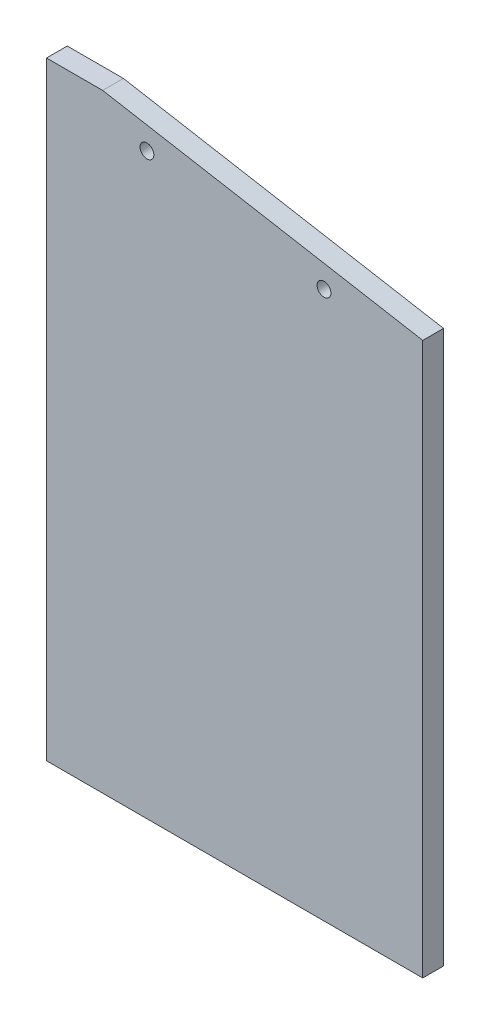
SolidWorks part; units mm, degrees
material "Pine"
ref_plane "Front Plane" through (0, 0, 0) normal (0, 0, 1) x (1, 0, 0)
ref_plane "Top Plane" through (0, 0, 0) normal (0, 1, 0) x (1, 0, 0)
ref_plane "Right Plane" through (0, 0, 0) normal (1, 0, 0) x (0, 0, -1)
sketch "Sketch1" plane through (0, 0, 0) normal (0, 0, 1) x (1, 0, 0)
  line L0 (151.0236, 150.9529) -> (-32.6409, 183.3379)
  line L1 (-64.8764, 183.3379) -> (-32.6409, 183.3379)
  line L2 (-64.8764, 183.3379) -> (-64.8764, -413.5621)
  line L3 (-64.8764, -413.5621) -> (-32.6409, -413.5621)
  line L4 (151.0236, 150.9529) -> (151.0236, -381.1771)
  line L5 (151.0236, -115.1121) -> (-64.8764, -115.1121) construction
  line L6 (151.0236, -381.1771) -> (-32.6409, -413.5621)
  dimension "D1" = 532.13
  dimension "D2" = 215.9
  dimension "D3" = 170
  dimension "D4" = 596.9
extrude "Boss-Extrude1" add sketch "Sketch1" along normal blind 11.9062
hole_wizard "5/16 (0.3125) Diameter Hole1" positions "Sketch2" profile "Sketch3" hole size "5/16" standard "ANSI Inch" end condition through all
sketch "Sketch2" plane through (0, 0, 11.9062) normal (0, 0, 1) x (1, 0, 0)
  line L0 (151.0236, 150.9529) -> (-32.6409, 183.3379) construction
  line L1 (-32.6409, -413.5621) -> (151.0236, -381.1771) construction
  point P0 (94.3591, 148.0484)
  point P2 (-7.2409, 165.9633)
  point P4 (-7.2409, -396.1875)
  point P6 (94.3591, -378.2727)
  dimension "D1" = 12.7
  dimension "D2" = 12.7
  dimension "D3" = 12.7
  dimension "D4" = 12.7
  dimension "D5" = 101.6
  dimension "D6" = 25.4
sketch "Sketch3" plane through (94.3591, 148.0484, 11.9062) normal (1, 0, 0) x (0, -1, 0)
  line L0 (0, 0) -> (0, 11.9062)
  line L1 (0, 11.9062) -> (3.9687, 11.9062)
  line L2 (3.9687, 11.9062) -> (3.9687, 0)
  line L5 (3.9687, 0) -> (0, 0)
  line L11 (0, -6.35) -> (0, 107.95) construction
  dimension "Thru Hole Dia." = 7.9375
  dimension "Thru Hole Depth" = 11.9062
sketch "Sketch4" plane through (0, 0, 0) normal (0, 0, -1) x (-1, 0, 0)
  line L0 (64.8764, -115.1121) -> (64.8764, -165.9121) construction
  line L1 (64.8764, -413.5621) -> (-155.6135, -413.5621)
  line L2 (64.8764, -413.5621) -> (64.8764, -165.9121)
  line L3 (64.8764, -165.9121) -> (-155.6135, -165.9121)
  line L4 (-155.6135, -413.5621) -> (-155.6135, -165.9121)
  line L5 (64.8764, 183.3379) -> (64.8764, -413.5621) construction
  dimension "D1" = 50.8
extrude "Cut-Extrude1" cut sketch "Sketch4" against normal through all
